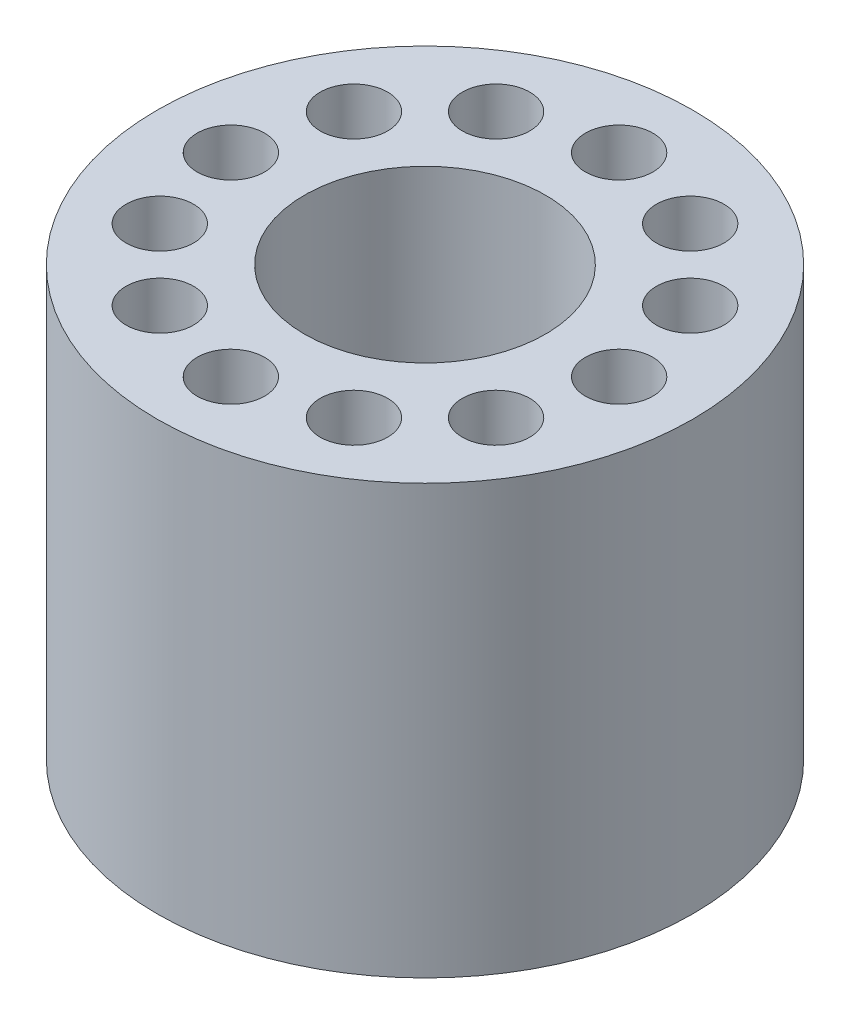
SolidWorks part; units mm, degrees
material "Silicon Rubber"
ref_plane "Front Plane" through (0, 0, 0) normal (0, 0, 1) x (1, 0, 0)
ref_plane "Top Plane" through (0, 0, 0) normal (0, 1, 0) x (1, 0, 0)
ref_plane "Right Plane" through (0, 0, 0) normal (1, 0, 0) x (0, 0, -1)
sketch "스케치1" plane through (0, 0, 0) normal (0, 1, 0) x (1, 0, 0)
  circle A0 centre (0, 0) radius 7.1438
  circle A1 centre (0, 0) radius 15.875
  dimension "D1" = 14.2875
  dimension "D2" = 31.75
extrude "보스-돌출1" add sketch "스케치1" along normal blind 25.4
sketch "스케치2" plane through (0, 25.4, 0) normal (0, 1, 0) x (1, 0, 0)
  line L0 (0, 7.1438) -> (0, 15.875) construction
  circle A0 centre (0, 0) radius 7.1438 construction
  circle A1 centre (0, 0) radius 15.875 construction
  circle A2 centre (0, 0) radius 7.1438 construction
  circle A3 centre (0, 0) radius 15.875 construction
  circle A4 centre (0, 11.5094) radius 2
  circle A5 centre (5.7547, 9.9674) radius 2
  circle A6 centre (9.9674, 5.7547) radius 2
  circle A7 centre (11.5094, 0) radius 2
  circle A8 centre (9.9674, -5.7547) radius 2
  circle A9 centre (5.7547, -9.9674) radius 2
  circle A10 centre (0, -11.5094) radius 2
  circle A11 centre (-5.7547, -9.9674) radius 2
  circle A12 centre (-9.9674, -5.7547) radius 2
  circle A13 centre (-11.5094, 0) radius 2
  circle A14 centre (-9.9674, 5.7547) radius 2
  circle A15 centre (-5.7547, 9.9674) radius 2
  point P34 (0, 0)
  dimension "D1" = 4
  dimension "D2" = 12
extrude "컷-돌출1" cut sketch "스케치2" against normal blind 25.4
